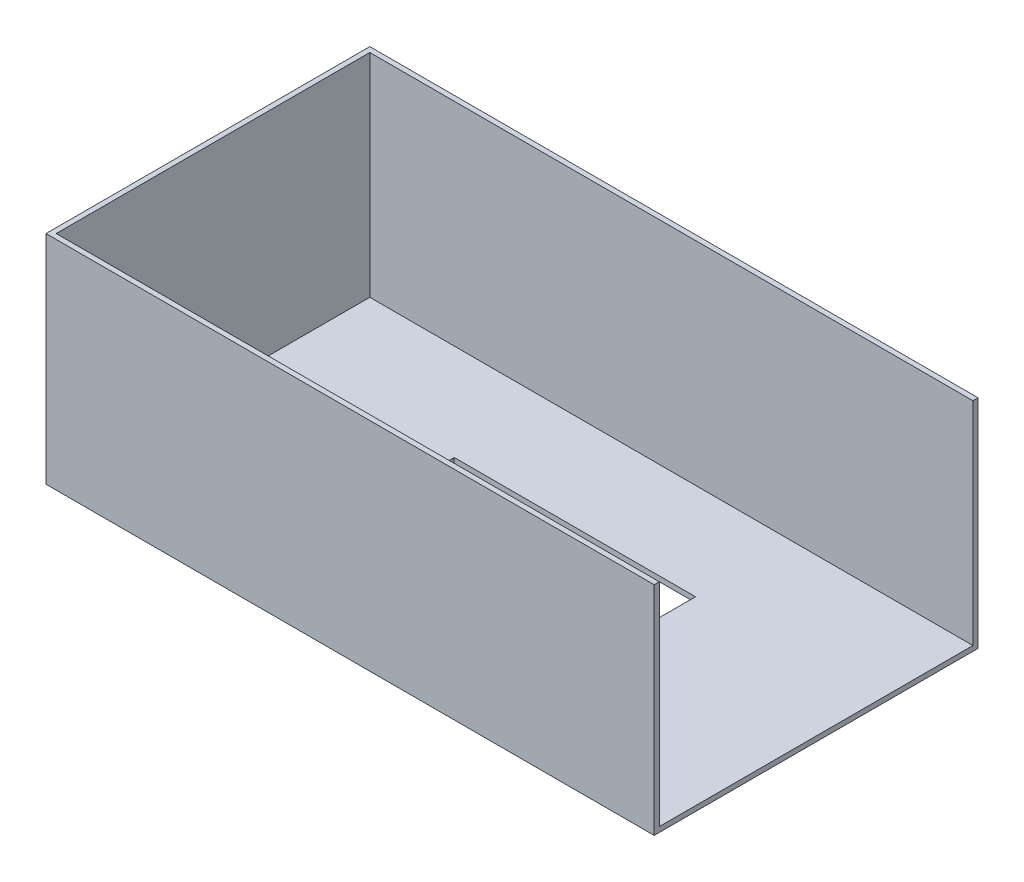
SolidWorks part; units mm, degrees
material "Aluminio 3105"
ref_plane "Alzado" through (0, 0, 0) normal (0, 0, 1) x (1, 0, 0)
ref_plane "Planta" through (0, 0, 0) normal (0, 1, 0) x (1, 0, 0)
ref_plane "Vista lateral" through (0, 0, 0) normal (1, 0, 0) x (0, 0, -1)
sketch "Croquis1" plane through (0, 0, 0) normal (0, 1, 0) x (1, 0, 0)
  line L1 (-125, -65) -> (125, -65)
  line L2 (-125, -65) -> (-125, 65)
  line L3 (-125, 65) -> (125, 65)
  line L4 (125, -65) -> (125, 65)
  line L5 (-125, -65) -> (125, 65) construction
  line L6 (-125, 65) -> (125, -65) construction
  point P0 (0, 0)
  dimension "D1" = 250
  dimension "D2" = 130
extrude "Saliente-Extruir1" add sketch "Croquis1" along normal mid plane 2.111
sketch "Croquis3" plane through (0, 0, 65) normal (0, 0, 1) x (1, 0, 0)
  line L1 (-125, -1.0555) -> (125, -1.0555)
  line L2 (-125, -1.0555) -> (-125, 88.9445)
  line L3 (-125, 88.9445) -> (125, 88.9445)
  line L4 (125, -1.0555) -> (125, 88.9445)
  dimension "D1" = 90
extrude "Saliente-Extruir2" add sketch "Croquis3" along normal blind 2.11
mirror "Simetría1" about plane through (0, 0, 0) normal (0, 0, 1) of "Saliente-Extruir2"
sketch "Croquis4" plane through (0, 1.0555, 0) normal (0, 1, 0) x (1, 0, 0)
  line L1 (50, 25) -> (-50, 25)
  line L2 (50, 25) -> (50, -25)
  line L3 (50, -25) -> (-50, -25)
  line L4 (-50, 25) -> (-50, -25)
  line L5 (50, 25) -> (-50, -25) construction
  line L6 (50, -25) -> (-50, 25) construction
  point P0 (0, 0)
  dimension "D1" = 100
  dimension "D2" = 50
extrude "Cortar-Extruir1" cut sketch "Croquis4" against normal up to surface (2.111 mm away) up to face at (0, -1.0555, 0)
sketch "Croquis5" plane through (-125, 0, 0) normal (-1, 0, 0) x (0, 0, 1)
  line L1 (-67.11, 88.9445) -> (67.11, 88.9445)
  line L2 (-67.11, 88.9445) -> (-67.11, -1.0555)
  line L3 (-67.11, -1.0555) -> (67.11, -1.0555)
  line L4 (67.11, 88.9445) -> (67.11, -1.0555)
extrude "Saliente-Extruir3" add sketch "Croquis5" along normal blind 2.11
